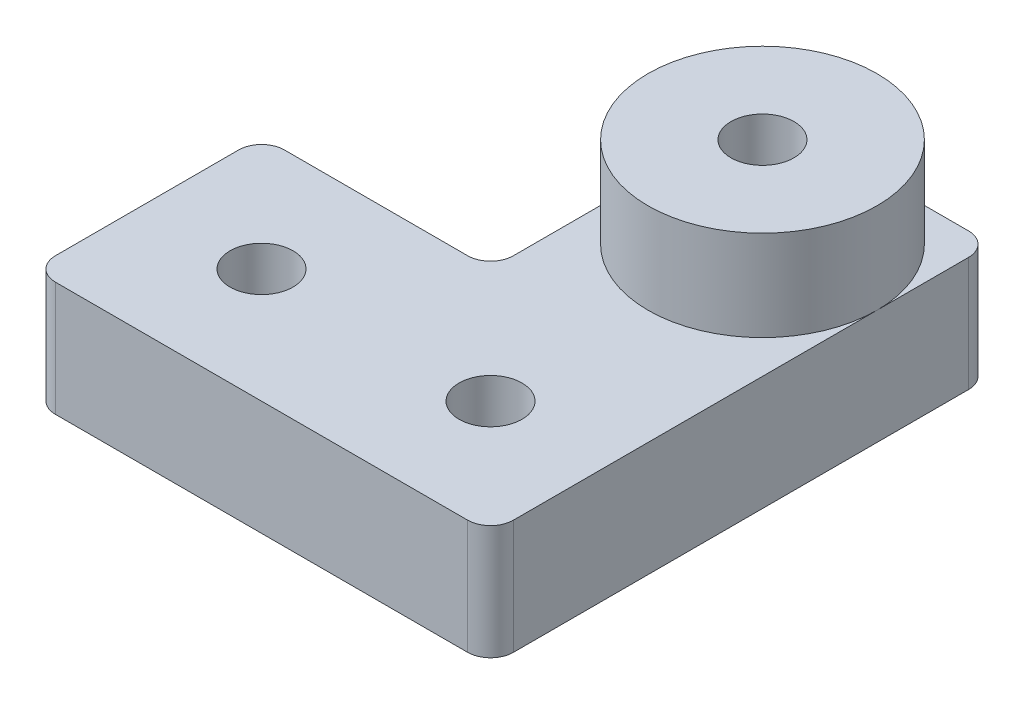
SolidWorks part; units mm, degrees
ref_plane "Front Plane" through (0, 0, 0) normal (0, 0, 1) x (1, 0, 0)
ref_plane "Top Plane" through (0, 0, 0) normal (0, 1, 0) x (1, 0, 0)
ref_plane "Right Plane" through (0, 0, 0) normal (1, 0, 0) x (0, 0, -1)
sketch "Sketch1" plane through (0, 0, 0) normal (0, 1, 0) x (1, 0, 0)
  line L0 (0, 0) -> (40, 0)
  line L1 (40, 0) -> (40, 43.75)
  line L2 (40, 43.75) -> (20, 43.75)
  line L3 (20, 43.75) -> (20, 20)
  line L4 (20, 20) -> (0, 20)
  line L5 (0, 20) -> (0, 0)
  dimension "D1" = 20
  dimension "D2" = 40
  dimension "D3" = 20
  dimension "D4" = 23.75
extrude "Boss-Extrude1" add sketch "Sketch1" along normal blind 10
sketch "Sketch2" plane through (0, 0, 0) normal (0, -1, 0) x (1, 0, 0)
  line L0 (0, -10) -> (40, -10)
  line L1 (0, -20) -> (0, 0) construction
  line L2 (40, 0) -> (40, -43.75) construction
  point P6 (10, -10)
  point P7 (30, -10)
  dimension "D1" = 10
  dimension "D2" = 10
hole_wizard "CBORE for M5 SHCS1" positions "Sketch3" profile "Sketch4" counterbore size "M5" standard "ANSI Metric" end condition through all
sketch "Sketch3" plane through (0, 0, 0) normal (0, -1, 0) x (-1, 0, 0)
  point P0 (-10, 10)
  point P3 (-30, 10)
sketch "Sketch4" plane through (10, 0, -10) normal (1, 0, 0) x (0, 0, -1)
  line L0 (0, 0) -> (0, 10)
  line L1 (0, 10) -> (2.75, 10)
  line L3 (2.75, 10) -> (2.75, 5)
  line L4 (5, 5) -> (2.75, 5)
  line L5 (5, 5) -> (5, 0.025)
  line L6 (5, 0.025) -> (5.025, 0)
  line L7 (5.025, 0) -> (0, 0)
  line L8 (-5, 0.025) -> (-5.025, 0) construction
  line L11 (0, -6.35) -> (0, 107.95) construction
  dimension "Thru Hole Dia." = 5.5
  dimension "Thru Hole Depth" = 10
  dimension "C'Bore Dia." = 10
  dimension "C'Bore Depth" = 5
  dimension "Near C'Sink Dia." = 10.05
  dimension "Near C'Sink Angle" = 90
fillet "Fillet1" radius 2 6 edges at (20, 5, -20) (20, 5, -43.75) (40, 5, -43.75) (0, 5, -20) (0, 5, 0) (40, 5, 0)
sketch "Sketch5" plane through (0, 10, 0) normal (0, 1, 0) x (1, 0, 0)
  line L0 (30, 43.75) -> (30, 0) construction
  line L1 (38, 43.75) -> (22, 43.75) construction
  line L2 (2, 0) -> (38, 0) construction
  line L3 (20, 33.75) -> (40, 33.75) construction
  circle A0 centre (30, 33.75) radius 1.5
  dimension "D1" = 3
  dimension "D2" = 10
sketch "Sketch6" plane through (0, 0, 0) normal (0, -1, 0) x (1, 0, 0)
  line L0 (38, -43.75) -> (22, -43.75) construction
  line L1 (34.7, -33.75) -> (32.35, -29.6797)
  line L2 (32.35, -29.6797) -> (27.65, -29.6797)
  line L3 (27.65, -29.6797) -> (25.3, -33.75)
  line L4 (25.3, -33.75) -> (27.65, -37.8203)
  line L5 (27.65, -37.8203) -> (32.35, -37.8203)
  line L6 (32.35, -37.8203) -> (34.7, -33.75)
  circle A0 centre (30, -33.75) radius 4.0703 construction
  dimension "D1" = 4.7
extrude "Cut-Extrude1" cut sketch "Sketch6" against normal blind 4.2
hole_wizard "M5 Clearance Hole1" positions "Sketch7" profile "Sketch8" hole size "M5" standard "ANSI Metric" end condition through all
sketch "Sketch7" plane through (0, 0, 0) normal (0, -1, 0) x (-1, 0, 0)
  point P0 (-30, 33.75)
sketch "Sketch8" plane through (30, 0, -33.75) normal (1, 0, 0) x (0, 0, -1)
  line L0 (0, 0) -> (0, 10)
  line L1 (0, 10) -> (2.75, 10)
  line L2 (2.75, 10) -> (2.75, 0.025)
  line L3 (2.75, 0.025) -> (2.775, 0)
  line L5 (2.775, 0) -> (0, 0)
  line L6 (-2.75, 0.025) -> (-2.775, 0) construction
  line L11 (0, -6.35) -> (0, 107.95) construction
  dimension "Thru Hole Dia." = 5.5
  dimension "Thru Hole Depth" = 10
  dimension "Near C'Sink Dia." = 5.55
  dimension "Near C'Sink Angle" = 90
sketch "Sketch9" plane through (0, 10, 0) normal (0, 1, 0) x (1, 0, 0)
  circle A0 centre (30, 33.75) radius 2.75 construction
  circle A1 centre (30, 33.75) radius 2.75
  circle A2 centre (30, 33.75) radius 10
  dimension "D1" = 20
extrude "Boss-Extrude2" add sketch "Sketch9" along normal blind 7.9
